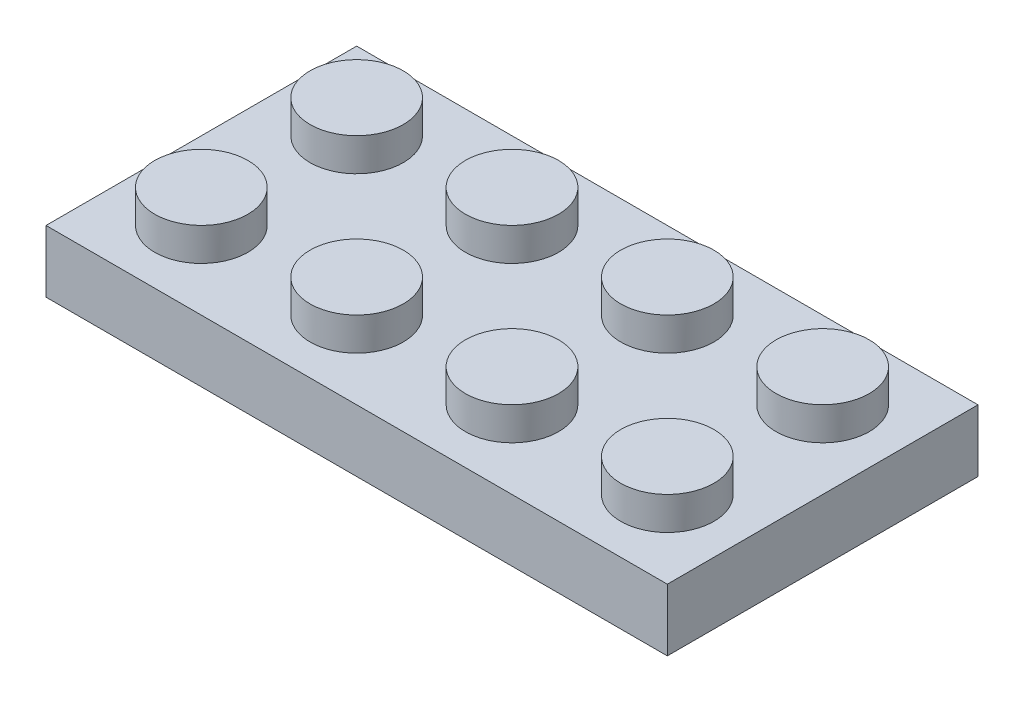
SolidWorks part; units mm, degrees
ref_plane "前基準面" through (0, 0, 0) normal (0, 0, 1) x (1, 0, 0)
ref_plane "上基準面" through (0, 0, 0) normal (0, 1, 0) x (1, 0, 0)
ref_plane "右基準面" through (0, 0, 0) normal (1, 0, 0) x (0, 0, -1)
sketch "草圖1" plane through (0, 0, 0) normal (0, 1, 0) x (1, 0, 0)
  line L1 (-4, -4) -> (4, -4)
  line L2 (-4, -4) -> (-4, 4)
  line L3 (-4, 4) -> (4, 4)
  line L4 (4, -4) -> (4, 4)
  line L5 (-4, -4) -> (4, 4) construction
  line L6 (-4, 4) -> (4, -4) construction
  point P0 (0, 0)
  dimension "width" = 8
  dimension "length" = 8
extrude "height" add sketch "草圖1" along normal blind 3.2
sketch "草圖2" plane through (0, 3.2, 0) normal (0, 1, 0) x (1, 0, 0)
  circle A0 centre (0, 0) radius 2.4
  dimension "D1" = 4.8
extrude "填料-伸長2" add sketch "草圖2" along normal blind 1.7
pattern_linear "直線複製排列1" count 2 spacing 8 along (0, 0, 1) of "填料-伸長2", "height"
pattern_linear "直線複製排列2" count 4 spacing 8 along (1, 0, 0) of "直線複製排列1", "height", "填料-伸長2"
shell "薄殼1" thickness 1.6
sketch "草圖3" plane through (0, 1.6, 0) normal (0, -1, 0) x (1, 0, 0)
  line L1 (0, 0) -> (8, 0) construction
  line L2 (0, 0) -> (0, 8) construction
  line L3 (0, 8) -> (8, 8) construction
  line L4 (8, 0) -> (8, 8) construction
  line L5 (0, 0) -> (8, 8) construction
  line L6 (0, 8) -> (8, 0) construction
  circle A0 centre (4, 4) radius 3.255
  circle A1 centre (4, 4) radius 2.4
  point P0 (4, 4)
  dimension "D1" = 4.8
  dimension "D2" = 6.51
extrude "填料-伸長3" add sketch "草圖3" along normal up to surface (1.6 mm away) up to face at (12, 0, 4)
pattern_linear "直線複製排列3" count 3 spacing 8 along (1, 0, 0) of "填料-伸長3"
